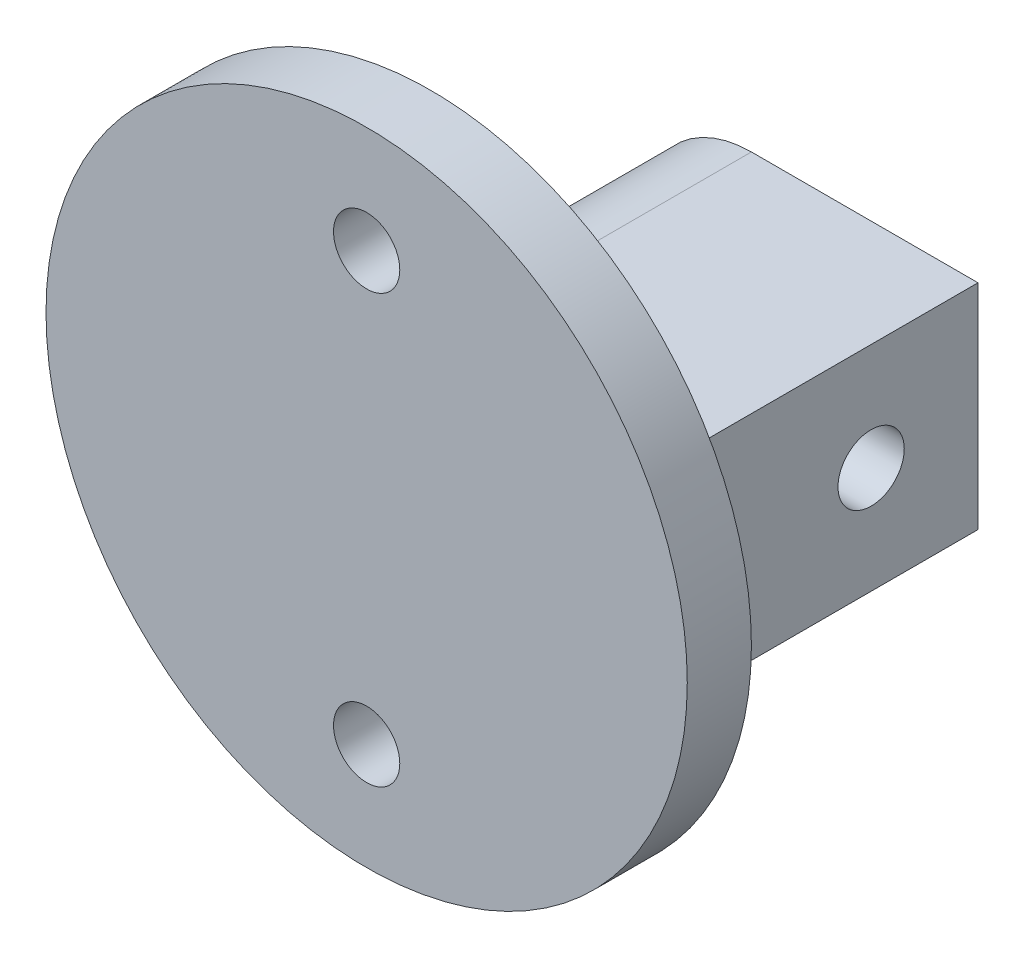
SolidWorks part; units mm, degrees
material "1060 Alloy"
ref_plane "Front Plane" through (0, 0, 0) normal (0, 0, 1) x (1, 0, 0)
ref_plane "Top Plane" through (0, 0, 0) normal (0, 1, 0) x (1, 0, 0)
ref_plane "Right Plane" through (0, 0, 0) normal (1, 0, 0) x (0, 0, -1)
sketch "Sketch1" plane through (0, 0, 0) normal (0, 0, 1) x (1, 0, 0)
  circle A1 centre (0, 0) radius 5
  dimension "D2" = 10
extrude "Boss-Extrude1" add sketch "Sketch1" along normal blind 15
sketch "Sketch2" plane through (0, 0, 15) normal (0, 0, 1) x (1, 0, 0)
  line L0 (0, 10) -> (0, 0) construction
  circle A0 centre (0, 0) radius 15
  circle A1 centre (0, 10) radius 1.55
  circle A6 centre (0, -10) radius 1.55
  circle A9 centre (10, 0) radius 1.55 [skipped]
  circle A10 centre (-10, 0) radius 1.55 [skipped]
  point P21 (0, 0)
  dimension "D1" = 30
  dimension "D3" = 3.1
  dimension "D4" = 10
  dimension "D2" = 4
extrude "Boss-Extrude3" add sketch "Sketch2" along normal blind 3
sketch "Sketch4" plane through (0, 0, 0) normal (0, 0, -1) x (-1, 0, 0)
  circle A0 centre (0, 0) radius 2.6
  dimension "D1" = 5.2
extrude "Cut-Extrude2" cut sketch "Sketch4" against normal blind 15
sketch "Sketch13" plane through (0, 0, 15) normal (0, 0, -1) x (-1, 0, 0)
  line L0 (0, 0) -> (-15, 0) construction
  line L1 (-10.6, -5) -> (-10.6, 5)
  line L2 (-7.6, 2.85) -> (-5, 2.85) construction
  line L3 (-7.6, 2.85) -> (-7.6, -2.85) construction
  line L4 (-7.6, -2.85) -> (-5, -2.85) construction
  line L5 (-5, 2.85) -> (-5, -2.85) construction
  line L6 (-6.3, -2.85) -> (-6.3, 2.85) construction
  line L7 (-7.6, 0) -> (-5, 0) construction
  line L8 (0, 5) -> (-10.6, 5)
  line L9 (0, -5) -> (-10.6, -5)
  circle A0 centre (0, 0) radius 15 construction
  circle A1 centre (0, 0) radius 5 construction
  circle A2 centre (0, 0) radius 5 construction
  arc A3 (0, 5) -> (0, -5) centre (0, 0) ccw
  point P6 (-6.3, 0)
  point P20 (-10.6, 0)
  circle M7 centre (0, 0) radius 5
  dimension "D1" = 2.6
  dimension "D2" = 5.7
  dimension "D3" = 3
extrude "Boss-Extrude7" add sketch "Sketch13" along normal up to surface (15 mm away) contours L9 L8 L1 M7 up to face at (-2.6, 0, 0)
sketch "Sketch14" plane through (0, 0, 0) normal (0, 0, -1) x (-1, 0, 0)
  line L1 (-7.6, 2.85) -> (-5, 2.85)
  line L2 (-7.6, 2.85) -> (-7.6, -2.85)
  line L3 (-7.6, -2.85) -> (-5, -2.85)
  line L4 (-5, 2.85) -> (-5, -2.85)
  line L5 (-6.3, -2.85) -> (-6.3, 2.85) construction
  line L6 (-7.6, 0) -> (-5, 0) construction
  point P0 (-6.3, 0)
extrude "Cut-Extrude7" cut sketch "Sketch14" against normal blind 8.3
sketch "Sketch15" plane through (10.6, 0, 0) normal (1, 0, 0) x (0, 0, -1)
  circle A0 centre (-5, 0) radius 1.55
  dimension "D1" = 3.1
  dimension "D2" = 5
extrude "Cut-Extrude8" cut sketch "Sketch15" against normal up to surface (8 mm away)
